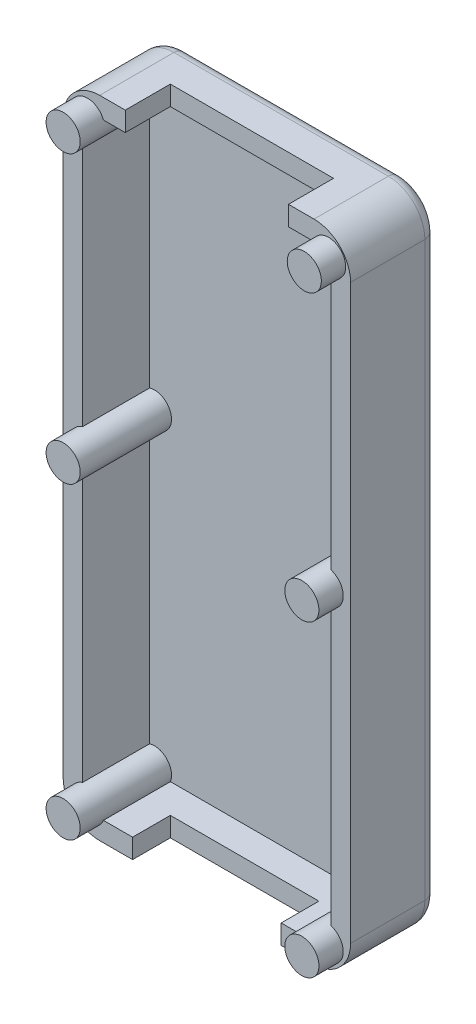
SolidWorks part; units mm, degrees
ref_plane "Front Plane" through (0, 0, 0) normal (0, 0, 1) x (1, 0, 0)
ref_plane "Top Plane" through (0, 0, 0) normal (0, 1, 0) x (1, 0, 0)
ref_plane "Right Plane" through (0, 0, 0) normal (1, 0, 0) x (0, 0, -1)
sketch "Sketch1" plane through (0, 0, 0) normal (0, 0, 1) x (1, 0, 0)
  line L1 (-40.6184, -1.5264) -> (-17.0184, -1.5264)
  line L2 (-40.6184, -1.5264) -> (-40.6184, -54.5264)
  line L3 (-40.6184, -54.5264) -> (-17.0184, -54.5264)
  line L4 (-17.0184, -1.5264) -> (-17.0184, -54.5264)
extrude "Boss-Extrude2" add sketch "Sketch1" along normal blind 7.1
shell "Shell1" thickness 1.6
fillet "Fillet2" radius 3 4 edges at (-17.0184, -1.5264, 3.55) (-17.0184, -54.5264, 3.55) (-40.6184, -54.5264, 3.55) (-40.6184, -1.5264, 3.55)
sketch "Sketch7" plane through (0, 0, 7.1) normal (0, 0, 1) x (1, 0, 0)
  line L6 (-40.6184, -4.5264) -> (-40.6184, -51.5264) construction
  line L7 (-17.0184, -51.5264) -> (-17.0184, -4.5264) construction
  line L8 (-39.0184, -52.9264) -> (-18.6184, -52.9264) construction
  line L9 (-34.9184, -52.9264) -> (-22.7184, -52.9264)
  line L10 (-34.9184, -52.9264) -> (-34.9184, -54.5264)
  line L11 (-34.9184, -54.5264) -> (-22.7184, -54.5264)
  line L12 (-22.7184, -52.9264) -> (-22.7184, -54.5264)
  line L13 (-37.6184, -54.5264) -> (-20.0184, -54.5264) construction
  dimension "D3" = 5.7
  dimension "D4" = 5.7
extrude "Cut-Extrude1" cut sketch "Sketch7" against normal blind 3.1 contours L9 L12 L11 L10
sketch "Sketch8" plane through (0, 0, 7.1) normal (0, 0, 1) x (1, 0, 0)
  line L0 (-20.0184, -1.5264) -> (-37.6184, -1.5264) construction
  line L1 (-35.5184, -1.5264) -> (-22.1184, -1.5264)
  line L2 (-35.5184, -1.5264) -> (-35.5184, -3.1264)
  line L3 (-35.5184, -3.1264) -> (-22.1184, -3.1264)
  line L4 (-22.1184, -1.5264) -> (-22.1184, -3.1264)
  line L5 (-18.6184, -3.1264) -> (-39.0184, -3.1264) construction
  line L6 (-40.6184, -4.5264) -> (-40.6184, -51.5264) construction
  line L7 (-17.0184, -51.5264) -> (-17.0184, -4.5264) construction
  dimension "D1" = 5.1
  dimension "D2" = 5.1
extrude "Cut-Extrude2" cut sketch "Sketch8" against normal blind 3.7
sketch "Sketch10" plane through (0, 0, 7.1) normal (0, 0, 1) x (1, 0, 0)
  circle A6 centre (-38.6184, -52.4264) radius 1.4
  circle A7 centre (-19.0184, -52.4264) radius 1.4
  circle A8 centre (-38.6184, -27.1264) radius 1.4
  circle A9 centre (-19.0184, -27.1264) radius 1.4
  circle A10 centre (-18.8184, -3.6264) radius 1.4
  circle A11 centre (-38.6184, -3.6264) radius 1.4
fillet "Fillet3" radius 1 8 edges at (-39.7397, -2.4051, 0) (-28.8184, -1.5264, 0) (-17.897, -2.4051, 0) (-17.0184, -28.0264, 0) (-17.897, -53.6477, 0) (-28.8184, -54.5264, 0) (-39.7397, -53.6477, 0) (-40.6184, -28.0264, 0)
extrude "Boss-Extrude4" add sketch "Sketch10" against normal blind 6.5 and the other way blind 2
